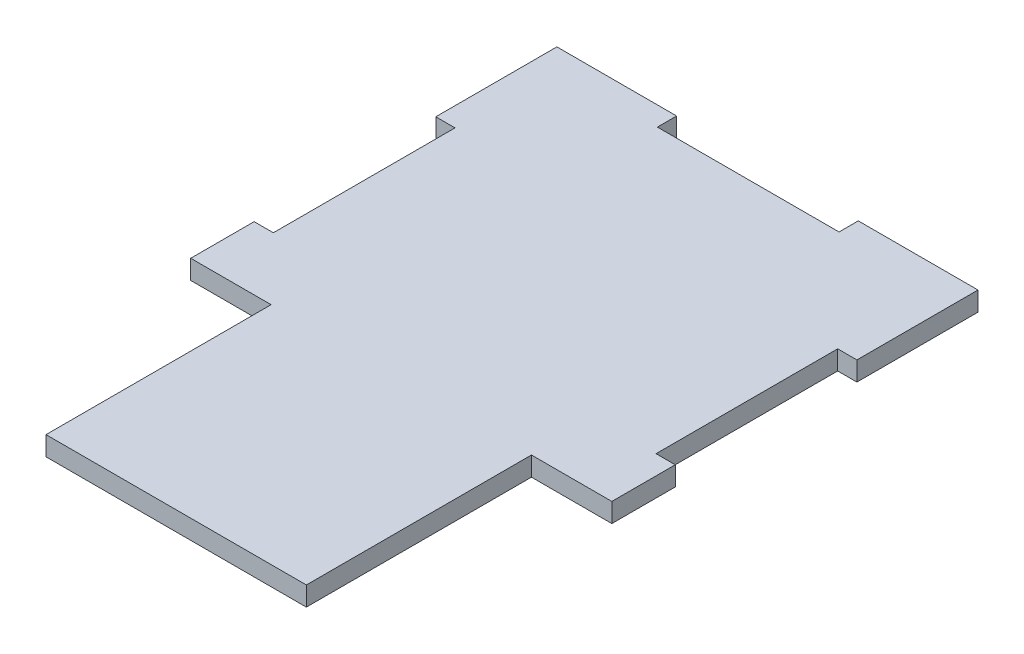
SolidWorks part; units mm, degrees
ref_plane "Front Plane" through (0, 0, 0) normal (0, 0, 1) x (1, 0, 0)
ref_plane "Top Plane" through (0, 0, 0) normal (0, 1, 0) x (1, 0, 0)
ref_plane "Right Plane" through (0, 0, 0) normal (1, 0, 0) x (0, 0, -1)
sketch "Sketch1" plane through (0, 0, 0) normal (0, 1, 0) x (1, 0, 0)
  line L0 (19.775, 91.3) -> (19.775, 94.475)
  line L1 (0, 0) -> (69.55, 0)
  line L2 (0, 0) -> (0, 94.475)
  line L3 (0, 94.475) -> (69.55, 94.475)
  line L4 (69.55, 0) -> (69.55, 94.475)
  line L5 (0, 0) -> (13.275, 0)
  line L6 (0, 0) -> (0, 34)
  line L7 (0, 34) -> (13.275, 34)
  line L8 (13.275, 0) -> (13.275, 34)
  line L9 (69.55, 0) -> (56.275, 0)
  line L10 (69.55, 0) -> (69.55, 34)
  line L11 (69.55, 34) -> (56.275, 34)
  line L12 (56.275, 0) -> (56.275, 34)
  line L13 (19.775, 91.3) -> (49.775, 91.3)
  line L14 (19.775, 94.475) -> (49.775, 94.475)
  line L15 (49.775, 91.3) -> (49.775, 94.475)
  line L16 (19.775, 91.3) -> (49.775, 94.475) construction
  line L17 (19.775, 94.475) -> (49.775, 91.3) construction
  line L19 (13.275, 0) -> (56.275, 0)
  line L20 (13.275, 0) -> (13.275, -3.175)
  line L21 (13.275, -3.175) -> (56.275, -3.175)
  line L22 (56.275, 0) -> (56.275, -3.175)
  line L23 (3.175, 74.475) -> (0, 74.475)
  line L24 (3.175, 74.475) -> (3.175, 44.475)
  line L25 (3.175, 44.475) -> (0, 44.475)
  line L26 (0, 74.475) -> (0, 44.475)
  line L27 (3.175, 74.475) -> (0, 44.475) construction
  line L28 (3.175, 44.475) -> (0, 74.475) construction
  line L29 (66.375, 44.475) -> (69.55, 44.475)
  line L30 (66.375, 44.475) -> (66.375, 74.475)
  line L31 (66.375, 74.475) -> (69.55, 74.475)
  line L32 (69.55, 44.475) -> (69.55, 74.475)
  line L33 (66.375, 44.475) -> (69.55, 74.475) construction
  line L34 (66.375, 74.475) -> (69.55, 44.475) construction
  ellipse E0 centre (34.775, 57.724) end of major axis (27.275, 57.724) minor radius 5
  point P12 (1.5875, 59.475)
  point P18 (34.775, 94.475)
  point P19 (34.775, 92.8875)
  point P30 (67.9625, 59.475)
  dimension "D1" = 69.55
  dimension "D2" = 94.475
  dimension "D3" = 34
  dimension "D4" = 43
  dimension "D5" = 10
  dimension "D6" = 15
  dimension "D7" = 3.175
  dimension "D8" = 30
  dimension "D9" = 3.175
  dimension "D10" = 3.175
  dimension "D11" = 30
  dimension "D12" = 20
extrude "Boss-Extrude1" add sketch "Sketch1" along normal blind 3.175 contours L1 L12 L11 L4 L3 L2 L7 L8 | E0 | L22 L1 L20 L21
